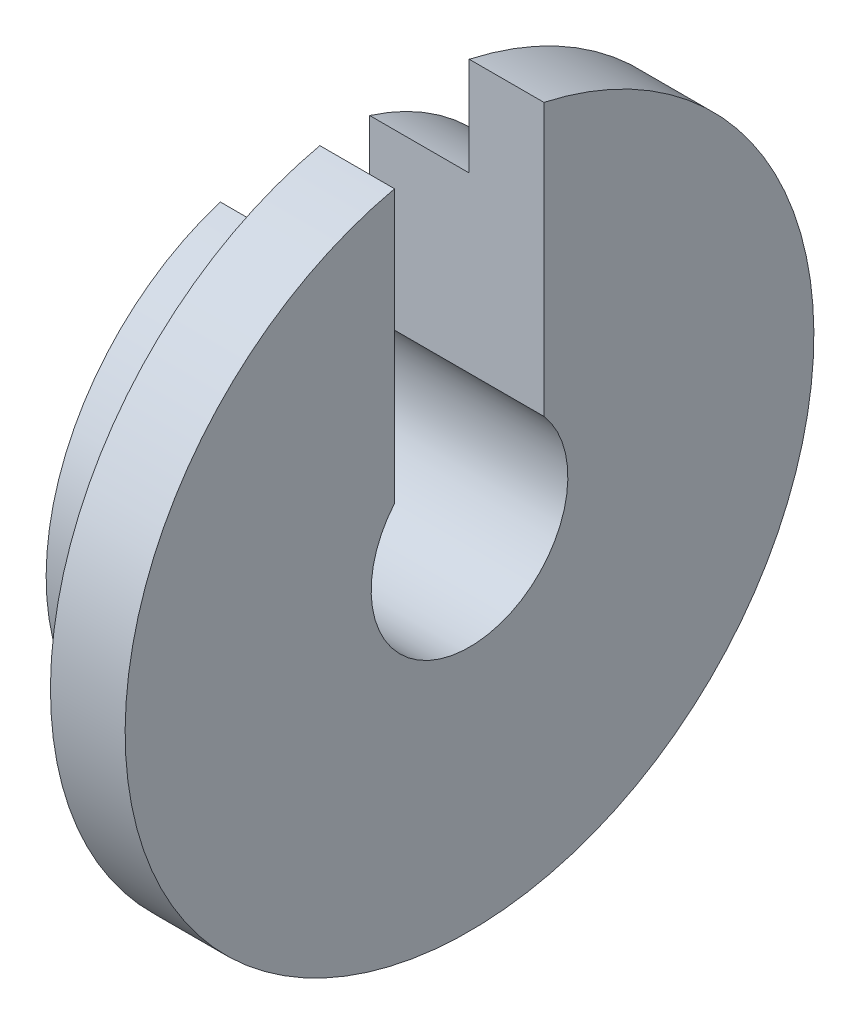
SolidWorks part; units mm, degrees
ref_plane "Front Plane" through (0, 0, 0) normal (0, 0, 1) x (1, 0, 0)
ref_plane "Top Plane" through (0, 0, 0) normal (0, 1, 0) x (1, 0, 0)
ref_plane "Right Plane" through (0, 0, 0) normal (1, 0, 0) x (0, 0, -1)
sketch "Sketch1" plane through (0, 0, 0) normal (1, 0, 0) x (0, 0, -1)
  line L2 (0.7593, 3.4301) -> (0.7593, 0.6558)
  line L4 (-0.7647, 3.4289) -> (-0.7647, 0.6495)
  arc A0 (-0.7647, 0.6495) -> (0.7593, 0.6558) centre (0, 0) ccw
  arc A1 (-0.7647, 3.4289) -> (0.7593, 3.4301) centre (0, 0) ccw
  point P4 (-0.0027, 2.8539)
  dimension "D1" = 1.524
  dimension "D2" = 1.0033
  dimension "D3" = 0.762
extrude "Boss-Extrude1" add sketch "Sketch1" along normal blind 0.762
sketch "Sketch3" plane through (0.762, 0, 0) normal (1, 0, 0) x (0, 0, -1)
  line L0 (-0.7647, 2.4233) -> (-0.7647, 0.6495)
  line L1 (-0.7647, 0.6495) -> (-0.7647, 3.4289) construction
  line L2 (0.7593, 2.425) -> (0.7593, 0.6558)
  line L3 (0.7593, 3.4301) -> (0.7593, 0.6558) construction
  arc A0 (-0.7647, 2.4233) -> (0.7593, 2.425) centre (0, 0) ccw
  arc A1 (-0.7647, 0.6495) -> (0.7593, 0.6558) centre (0, 0) ccw
extrude "Boss-Extrude2" add sketch "Sketch3" against normal blind 1.778
